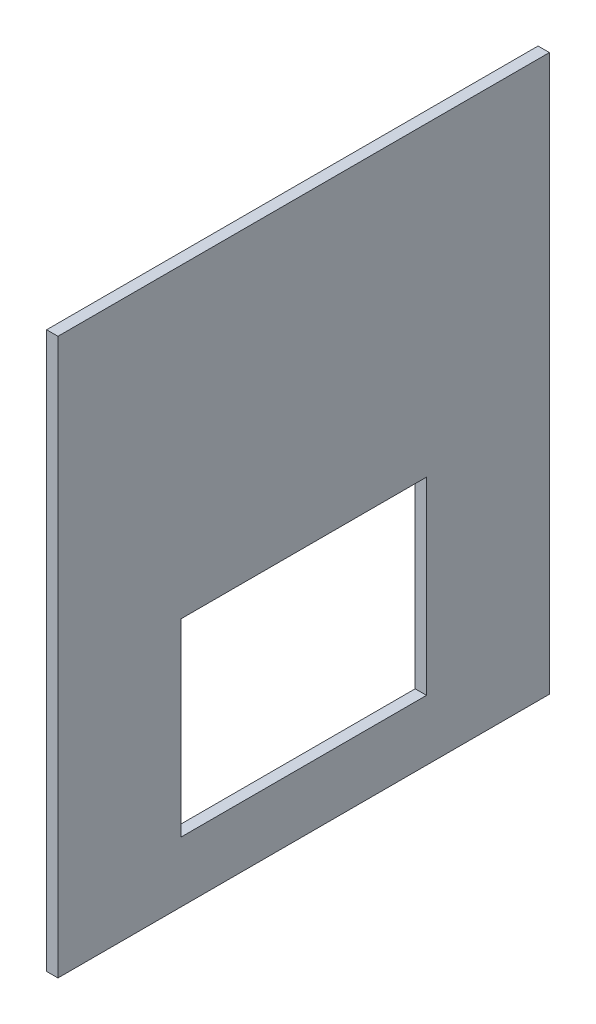
SolidWorks part; units mm, degrees
ref_plane "Front Plane" through (0, 0, 0) normal (0, 0, 1) x (1, 0, 0)
ref_plane "Top Plane" through (0, 0, 0) normal (0, 1, 0) x (1, 0, 0)
ref_plane "Right Plane" through (0, 0, 0) normal (1, 0, 0) x (0, 0, -1)
sketch "Sketch1" plane through (0, 0, 0) normal (1, 0, 0) x (0, 0, -1)
  line L1 (0, 0) -> (130, 0)
  line L2 (0, 0) -> (0, 147)
  line L3 (0, 147) -> (130, 147)
  line L4 (130, 0) -> (130, 147)
  line L5 (32.5, 66) -> (97.5, 66)
  line L6 (32.5, 66) -> (32.5, 16)
  line L7 (32.5, 16) -> (97.5, 16)
  line L8 (97.5, 66) -> (97.5, 16)
  dimension "D1" = 147
  dimension "D2" = 130
  dimension "D3" = 65
  dimension "D4" = 50
  dimension "D5" = 16
  dimension "D6" = 32.5
extrude "Boss-Extrude2" add sketch "Sketch1" along normal blind 3
